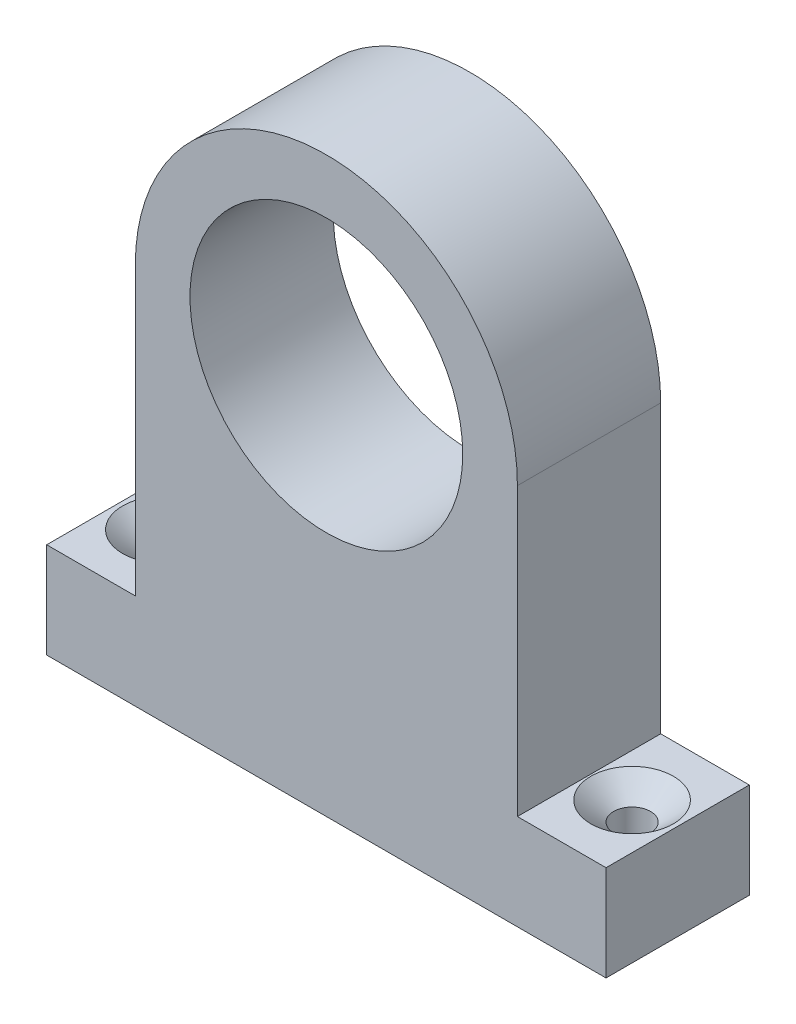
SolidWorks part; units mm, degrees
ref_plane "Front Plane" through (0, 0, 0) normal (0, 0, 1) x (1, 0, 0)
ref_plane "Top Plane" through (0, 0, 0) normal (0, 1, 0) x (1, 0, 0)
ref_plane "Right Plane" through (0, 0, 0) normal (1, 0, 0) x (0, 0, -1)
sketch "Sketch1" plane through (0, 19.05, 0) normal (0, 1, 0) x (1, 0, 0)
  line L0 (18.1316, -59.4106) -> (-18.1316, -59.4106) construction
  line L1 (-37.1816, -78.4606) -> (37.1816, -78.4606)
  line L2 (-37.1816, -78.4606) -> (-37.1816, -97.5106)
  line L3 (-37.1816, -97.5106) -> (37.1816, -97.5106)
  line L4 (37.1816, -78.4606) -> (37.1816, -97.5106)
  line L5 (-18.1316, -113.4106) -> (18.1316, -113.4106) construction
  line L6 (-18.1316, -113.4106) -> (18.1316, -113.4106) construction
  dimension "D1" = 19.05
  dimension "D2" = 19.05
  dimension "D3" = 19.05
  dimension "D4" = 19.05
extrude "Boss-Extrude2" add sketch "Sketch1" along normal blind 76.2
sketch "Sketch2" plane through (0, 0, 97.5106) normal (0, 0, 1) x (1, 0, 0)
  line L0 (-37.1816, 95.25) -> (37.1816, 95.25) construction
  line L1 (-37.1816, 31.75) -> (37.1816, 31.75)
  line L4 (0, 95.25) -> (0, 69.85) construction
  line L5 (-25.4, 69.85) -> (-25.4, 31.75)
  line L6 (25.4, 69.85) -> (25.4, 31.75)
  line L8 (-37.1816, 19.05) -> (37.1816, 19.05)
  line L9 (37.1816, 19.05) -> (37.1816, 95.25)
  line L10 (37.1816, 95.25) -> (-37.1816, 95.25)
  line L11 (-37.1816, 95.25) -> (-37.1816, 19.05)
  line L12 (-37.1816, 19.05) -> (37.1816, 19.05)
  line L13 (37.1816, 19.05) -> (37.1816, 95.25)
  line L14 (37.1816, 95.25) -> (-37.1816, 95.25)
  line L15 (-37.1816, 95.25) -> (-37.1816, 19.05)
  circle A0 centre (0, 69.85) radius 18.1316 construction
  circle A1 centre (0, 69.85) radius 18.1316
  circle A2 centre (0, 69.85) radius 25.4
  line M8 (37.1816, 19.05) -> (37.1816, 95.25)
  line M9 (37.1816, 95.25) -> (-37.1816, 95.25)
  line M10 (-37.1816, 95.25) -> (-37.1816, 19.05)
  dimension "D2" = 12.7
  dimension "D1" = 0
extrude "Cut-Extrude1" cut sketch "Sketch2" against normal through all contours A2 L14 L1 L5 M10 | A2 L6 L1 M8 M9 | A1
hole_wizard "CSK for #8 Flat Head Machine Screw (100)1" positions "Sketch3" profile "Sketch4" countersink size "#8" standard "ANSI Inch" end condition through all
sketch "Sketch3" plane through (0, 31.75, 0) normal (0, 1, 0) x (1, 0, 0)
  point P0 (-31.125, -87.9856)
  point P1 (31.125, -87.9856)
sketch "Sketch4" plane through (-31.125, 31.75, 87.9856) normal (1, 0, 0) x (0, 0, 1)
  line L0 (0, 0) -> (0, 12.7)
  line L1 (0, 12.7) -> (2.4574, 12.7)
  line L2 (2.4574, 12.7) -> (2.4574, 2.5416)
  line L3 (2.4574, 2.5416) -> (5.4864, 0)
  line L5 (5.4864, 0) -> (0, 0)
  line L6 (-2.4574, 2.5416) -> (-5.4864, 0) construction
  line L11 (0, -6.35) -> (0, 107.95) construction
  dimension "Thru Hole Dia." = 4.9149
  dimension "Thru Hole Depth" = 12.7
  dimension "Near C'Sink Dia." = 10.9728
  dimension "Near C'Sink Angle" = 100
